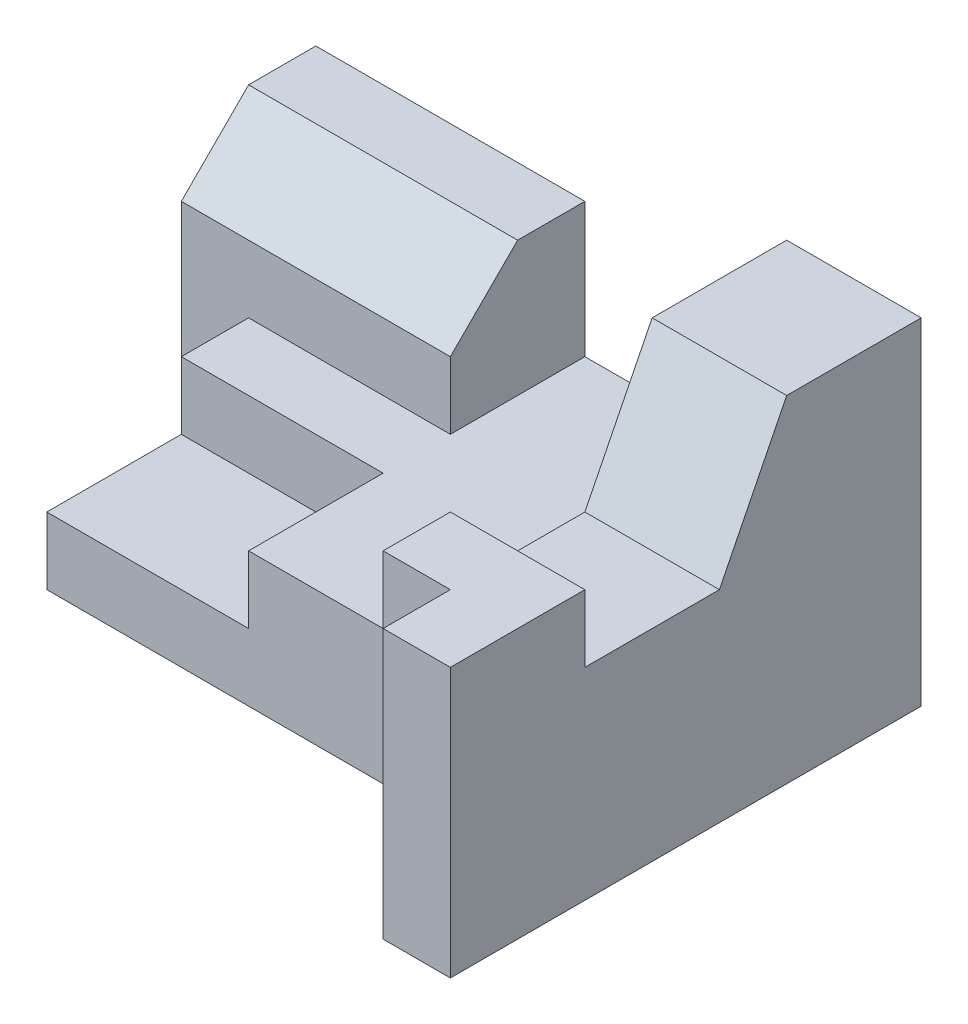
SolidWorks part; units mm, degrees
ref_plane "Front Plane" through (0, 0, 0) normal (0, 0, 1) x (1, 0, 0)
ref_plane "Top Plane" through (0, 0, 0) normal (0, 1, 0) x (1, 0, 0)
ref_plane "Right Plane" through (0, 0, 0) normal (1, 0, 0) x (0, 0, -1)
sketch "Sketch1" plane through (0, 0, 0) normal (0, 1, 0) x (1, 0, 0)
  line L1 (-3, -2.5) -> (3, -2.5)
  line L2 (-3, -2.5) -> (-3, 2.5)
  line L3 (-3, 2.5) -> (3, 2.5)
  line L4 (3, -2.5) -> (3, 2.5)
  line L5 (-3, -2.5) -> (3, 2.5) construction
  line L6 (-3, 2.5) -> (3, -2.5) construction
  point P0 (0, 0)
  dimension "D1" = 6
  dimension "D2" = 5
extrude "Boss-Extrude1" add sketch "Sketch1" along normal blind 2
sketch "Sketch2" plane through (0, 0, 0) normal (0, 1, 0) x (1, 0, 0)
  line L0 (3, 2.5) -> (-3, 2.5) construction
  line L1 (0, 2.5) -> (-4, 2.5)
  line L2 (0, 2.5) -> (0, 0.5)
  line L3 (0, 0.5) -> (-4, 0.5)
  line L4 (-4, 2.5) -> (-4, 0.5)
  line L5 (-3, 2.5) -> (-3, -2.5) construction
  dimension "D1" = 2
  dimension "D2" = 4
  dimension "D3" = 1
extrude "Boss-Extrude2" add sketch "Sketch2" along normal blind 4
chamfer "Chamfer1" distance 1 1 edges at (-2, 4, -0.5)
sketch "Sketch3" plane through (0, 0, 0) normal (0, 1, 0) x (1, 0, 0)
  line L0 (3, 2.5) -> (5, 2.5)
  line L1 (5, 2.5) -> (5, -4.5)
  line L2 (5, -4.5) -> (4, -4.5)
  line L3 (4, -4.5) -> (4, -3.5)
  line L4 (4, -3.5) -> (3, -3.5)
  line L5 (3, -3.5) -> (3, 2.5)
  dimension "D1" = 1
  dimension "D2" = 7
  dimension "D3" = 1
  dimension "D4" = 2
extrude "Boss-Extrude3" add sketch "Sketch3" along normal blind 5
sketch "Sketch5" plane through (3, 0, 0) normal (-1, 0, 0) x (0, 0, 1)
  line L0 (-0.5, 5) -> (0.5, 3)
  line L1 (-2.5, 5) -> (3.5, 5) construction
  line L2 (0.5, 3) -> (2.5, 3)
  line L3 (2.5, 3) -> (2.5, 4)
  line L4 (2.5, 4) -> (5.8633, 4)
  line L5 (5.8633, 4) -> (5.8633, 5.5367)
  line L6 (5.8633, 5.5367) -> (-0.5, 5)
  dimension "D1" = 2
  dimension "D2" = 1
  dimension "D3" = 2
  dimension "D4" = 1
  dimension "D5" = 2
extrude "Cut-Extrude1" cut sketch "Sketch5" against normal blind 5
sketch "Sketch6" plane through (0, 2, 0) normal (0, 1, 0) x (1, 0, 0)
  line L1 (-3, -2.5) -> (0, -2.5)
  line L2 (-3, -2.5) -> (-3, -0.5)
  line L3 (-3, -0.5) -> (0, -0.5)
  line L4 (0, -2.5) -> (0, -0.5)
  dimension "D1" = 3
  dimension "D2" = 2
extrude "Cut-Extrude2" cut sketch "Sketch6" against normal blind 1
